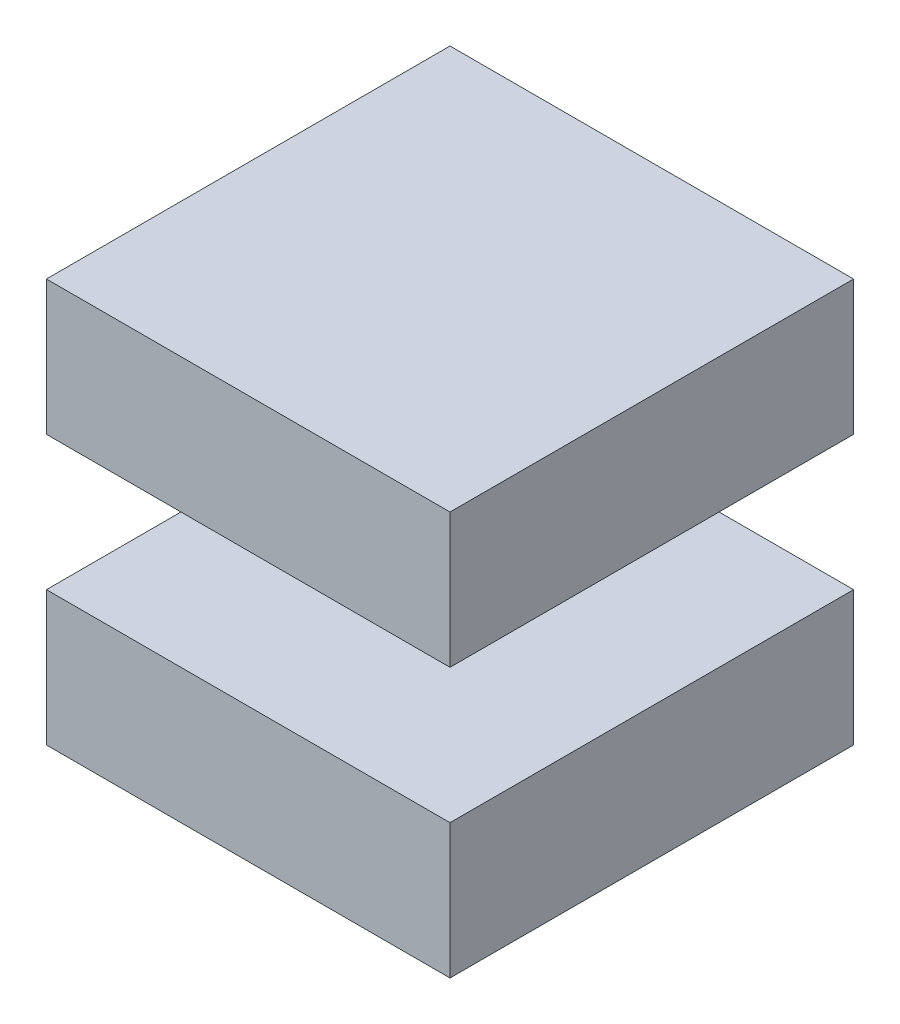
SolidWorks part; units mm, degrees
ref_plane "Front Plane" through (0, 0, 0) normal (0, 0, 1) x (1, 0, 0)
ref_plane "Top Plane" through (0, 0, 0) normal (0, 1, 0) x (1, 0, 0)
ref_plane "Right Plane" through (0, 0, 0) normal (1, 0, 0) x (0, 0, -1)
sketch "Sketch1" plane through (0, 0, 0) normal (0, 0, 1) x (1, 0, 0)
  line L1 (0, 0) -> (60, 0)
  line L2 (0, 0) -> (0, 60)
  line L3 (0, 60) -> (60, 60)
  line L4 (60, 0) -> (60, 60)
  dimension "D1" = 60
  dimension "D2" = 60
extrude "Boss-Extrude1" add sketch "Sketch1" along normal blind 60
sketch "Sketch2" plane through (0, 0, 60) normal (0, 0, 1) x (1, 0, 0)
  line L0 (0, 60) -> (0, 0) construction
  line L1 (0, 40) -> (20, 40)
  line L2 (0, 40) -> (0, 20)
  line L3 (0, 20) -> (20, 20)
  line L4 (20, 40) -> (20, 20)
  line L5 (60, 0) -> (60, 60) construction
  line L6 (60, 40) -> (40, 40)
  line L7 (60, 40) -> (60, 20)
  line L8 (60, 20) -> (40, 20)
  line L9 (40, 40) -> (40, 20)
  line L10 (60, 60) -> (0, 60) construction
  dimension "D1" = 20
  dimension "D2" = 20
  dimension "D3" = 20
  dimension "D4" = 20
  dimension "D5" = 20
  dimension "D6" = 20
extrude "Cut-Extrude1" cut sketch "Sketch2" against normal blind 60
sketch "Sketch3" plane through (0, 0, 0) normal (-1, 0, 0) x (0, 0, 1)
  line L0 (60, 60) -> (0, 60) construction
  line L1 (40, 60) -> (20, 60)
  line L2 (40, 60) -> (40, 40)
  line L3 (40, 40) -> (20, 40)
  line L4 (20, 60) -> (20, 40)
  line L5 (0, 40) -> (60, 40) construction
  line L6 (60, 0) -> (0, 0) construction
  line L7 (20, 0) -> (40, 0)
  line L8 (20, 0) -> (20, 20)
  line L9 (20, 20) -> (40, 20)
  line L10 (40, 0) -> (40, 20)
  line L11 (0, 20) -> (60, 20) construction
  line L12 (0, 20) -> (0, 40) construction
  dimension "D1" = 20
  dimension "D2" = 20
  dimension "D3" = 20
  dimension "D4" = 20
extrude "Cut-Extrude2" cut sketch "Sketch3" against normal blind 20
sketch "Sketch4" plane through (20, 0, 0) normal (-1, 0, 0) x (0, 0, 1)
  line L1 (20, 20) -> (0, 20)
  line L2 (20, 20) -> (20, 40)
  line L3 (20, 40) -> (0, 40)
  line L4 (0, 20) -> (0, 40)
  line L5 (40, 20) -> (60, 20)
  line L6 (40, 20) -> (40, 40)
  line L7 (40, 40) -> (60, 40)
  line L8 (60, 20) -> (60, 40)
extrude "Cut-Extrude3" cut sketch "Sketch4" against normal blind 20
sketch "Sketch5" plane through (20, 0, 0) normal (-1, 0, 0) x (0, 0, 1)
  line L0 (20, 60) -> (20, 40) construction
  line L1 (40, 60) -> (20, 60)
  line L2 (40, 60) -> (40, 40)
  line L3 (40, 40) -> (20, 40)
  line L4 (20, 60) -> (20, 40)
  line L5 (20, 20) -> (20, 40) construction
  line L7 (20, 20) -> (40, 20)
  line L8 (20, 20) -> (20, 0)
  line L9 (20, 0) -> (40, 0)
  line L10 (40, 20) -> (40, 0)
extrude "Boss-Extrude2" add sketch "Sketch5" along normal blind 20
